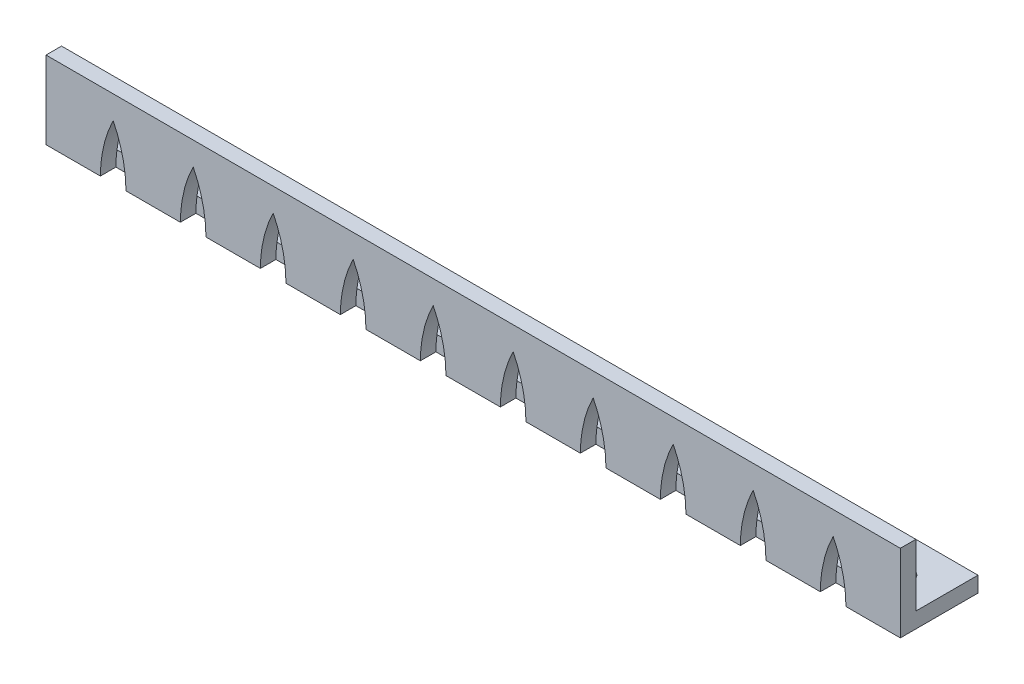
SolidWorks part; units mm, degrees
material "ABS"
ref_plane "Front Plane" through (0, 0, 0) normal (0, 0, 1) x (1, 0, 0)
ref_plane "Top Plane" through (0, 0, 0) normal (0, 1, 0) x (1, 0, 0)
ref_plane "Right Plane" through (0, 0, 0) normal (1, 0, 0) x (0, 0, -1)
ref_plane "Front Plane1" through (0, 0, 5) normal (0, 0, 1) x (1, 0, 0)
sketch "Sketch1" plane through (0, 0, 0) normal (0, 1, 0) x (1, 0, 0)
  line L0 (-55, 5) -> (55, -5) construction
  line L1 (-55, 5) -> (55, 5)
  line L2 (-55, 5) -> (-55, -5)
  line L3 (-55, -5) -> (55, -5)
  line L4 (55, 5) -> (55, -5)
  circle A0 centre (-50, 0) radius 1.5025
  circle A1 centre (-40, 0) radius 1.5025
  circle A2 centre (-30, 0) radius 1.5025
  circle A3 centre (-20, 0) radius 1.5025
  circle A4 centre (-10, 0) radius 1.5025
  circle A5 centre (0, 0) radius 1.5025
  circle A6 centre (10, 0) radius 1.5025
  circle A7 centre (20, 0) radius 1.5025
  circle A8 centre (30, 0) radius 1.5025
  circle A9 centre (40, 0) radius 1.5025
  circle A10 centre (50, 0) radius 1.5025
  dimension "D3" = 3.005
  dimension "D4" = 5
  dimension "D5" = 5
  dimension "D7" = 5
  dimension "D1" = 110
  dimension "D2" = 10
  dimension "D8" = 5
  dimension "D6" = 11
extrude "Boss-Extrude1" add sketch "Sketch1" along normal blind 10
sketch "Sketch2" plane through (0, 0, 0) normal (0, 0, 1) x (1, 0, 0)
  line L0 (55, 10) -> (55, 0) construction
  line L1 (-55, 10) -> (55, 10)
  line L2 (-55, 10) -> (-55, 2)
  line L3 (-55, 2) -> (55, 2)
  line L4 (55, 10) -> (55, 2)
  dimension "D1" = 8
extrude "Cut-Extrude1" cut sketch "Sketch2" against normal up to next and the other way blind 3
sketch "Sketch3" plane through (0, 0, 5) normal (0, 0, 1) x (1, 0, 0)
  line L0 (-47.175, 5) -> (-45.525, 5) construction
  line L1 (-55, 10) -> (-55, 0) construction
  line L2 (-37.7, 0) -> (-34.4, 0)
  line L3 (-55, 0) -> (55, 0) construction
  line L4 (-48, 0) -> (-44.7, 0)
  line L5 (-48, 10) -> (-48, 0) construction
  line L6 (-55, 10) -> (55, 10) construction
  line L7 (-46.35, 10) -> (-46.35, 0) construction
  line L8 (-44.7, 10) -> (-44.7, 0) construction
  line L9 (-47.175, 10) -> (-47.175, 0) construction
  line L10 (-45.525, 10) -> (-45.525, 0) construction
  line L11 (55, 10) -> (55, 0) construction
  line L12 (-27.4, 0) -> (-24.1, 0)
  line L13 (-17.1, 0) -> (-13.8, 0)
  line L14 (-6.8, 0) -> (-3.5, 0)
  line L15 (3.5, 0) -> (6.8, 0)
  line L16 (13.8, 0) -> (17.1, 0)
  line L17 (24.1, 0) -> (27.4, 0)
  line L18 (34.4, 0) -> (37.7, 0)
  line L19 (44.7, 0) -> (48, 0)
  spline S0 degree 2 poles (-46.35, 7) (-47.9651, 3.725) (-48, 0) knots 0 0 0 1 1 1
  spline S1 degree 2 poles (-46.35, 7) (-44.7349, 3.725) (-44.7, 0) knots 0 0 0 1 1 1
  spline S2 degree 2 poles (-36.05, 7) (-34.4349, 3.725) (-34.4, 0) knots 0 0 0 1 1 1
  spline S3 degree 2 poles (-36.05, 7) (-37.6651, 3.725) (-37.7, 0) knots 0 0 0 1 1 1
  spline S4 degree 2 poles (-25.75, 7) (-24.1349, 3.725) (-24.1, 0) knots 0 0 0 1 1 1
  spline S5 degree 2 poles (-25.75, 7) (-27.3651, 3.725) (-27.4, 0) knots 0 0 0 1 1 1
  spline S6 degree 2 poles (-15.45, 7) (-13.8349, 3.725) (-13.8, 0) knots 0 0 0 1 1 1
  spline S7 degree 2 poles (-15.45, 7) (-17.0651, 3.725) (-17.1, 0) knots 0 0 0 1 1 1
  spline S8 degree 2 poles (-5.15, 7) (-3.5349, 3.725) (-3.5, 0) knots 0 0 0 1 1 1
  spline S9 degree 2 poles (-5.15, 7) (-6.7651, 3.725) (-6.8, 0) knots 0 0 0 1 1 1
  spline S10 degree 2 poles (5.15, 7) (6.7651, 3.725) (6.8, 0) knots 0 0 0 1 1 1
  spline S11 degree 2 poles (5.15, 7) (3.5349, 3.725) (3.5, 0) knots 0 0 0 1 1 1
  spline S12 degree 2 poles (15.45, 7) (17.0651, 3.725) (17.1, 0) knots 0 0 0 1 1 1
  spline S13 degree 2 poles (15.45, 7) (13.8349, 3.725) (13.8, 0) knots 0 0 0 1 1 1
  spline S14 degree 2 poles (25.75, 7) (27.3651, 3.725) (27.4, 0) knots 0 0 0 1 1 1
  spline S15 degree 2 poles (25.75, 7) (24.1349, 3.725) (24.1, 0) knots 0 0 0 1 1 1
  spline S16 degree 2 poles (36.05, 7) (37.6651, 3.725) (37.7, 0) knots 0 0 0 1 1 1
  spline S17 degree 2 poles (36.05, 7) (34.4349, 3.725) (34.4, 0) knots 0 0 0 1 1 1
  spline S18 degree 2 poles (46.35, 7) (47.9651, 3.725) (48, 0) knots 0 0 0 1 1 1
  spline S19 degree 2 poles (46.35, 7) (44.7349, 3.725) (44.7, 0) knots 0 0 0 1 1 1
  point P0 (-46.35, 7)
  point P8 (48, 0)
  point P25 (120.1, 0)
  point P26 (140.7, 0)
  point P34 (58.3, 0)
  point P40 (68.6, 0)
  point P46 (78.9, 0)
  point P52 (89.2, 0)
  point P58 (99.5, 0)
  point P64 (130.4, 0)
  point P70 (109.8, 0)
  dimension "D1" = 7
  dimension "D2" = 7
  dimension "D3" = 1.65
  dimension "D4" = 1.65
  dimension "D5" = 0.825
  dimension "D6" = 0.825
  dimension "D7" = 5
  dimension "D8" = 7
  dimension "D9" = 10
extrude "Cut-Extrude2" cut sketch "Sketch3" against normal blind 2
